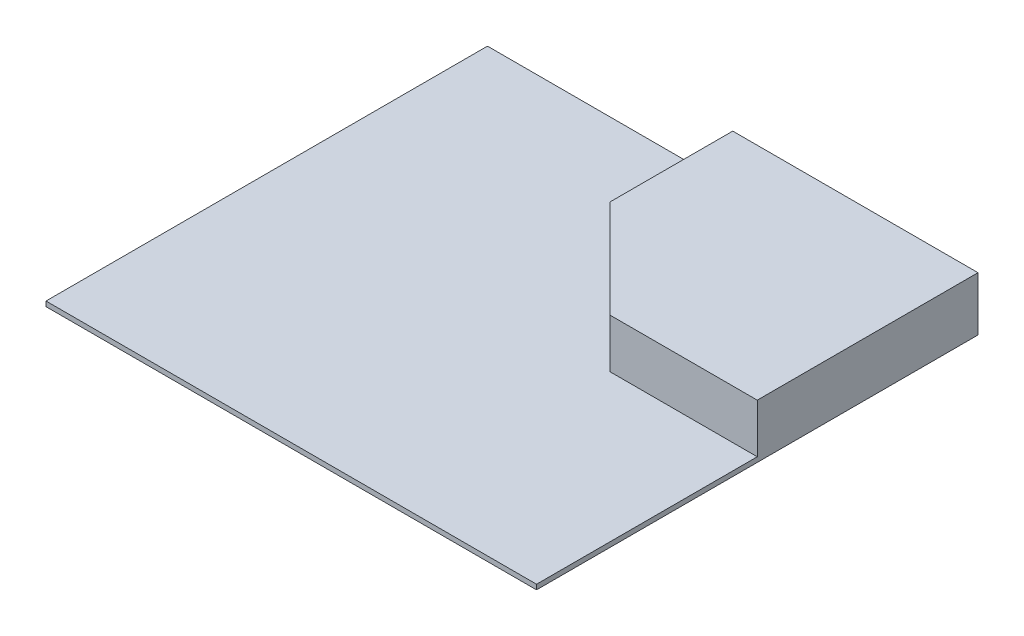
SolidWorks part; units mm, degrees
ref_plane "Front Plane" through (0, 0, 0) normal (0, 0, 1) x (1, 0, 0)
ref_plane "Top Plane" through (0, 0, 0) normal (0, 1, 0) x (1, 0, 0)
ref_plane "Right Plane" through (0, 0, 0) normal (1, 0, 0) x (0, 0, -1)
sketch "Sketch1" plane through (0, 0, 0) normal (0, 1, 0) x (1, 0, 0)
  line L1 (-500, 450) -> (500, 450)
  line L2 (-500, 450) -> (-500, -450)
  line L3 (-500, -450) -> (500, -450)
  line L4 (500, 450) -> (500, -450)
  line L5 (-500, 450) -> (500, -450) construction
  line L6 (-500, -450) -> (500, 450) construction
  point P0 (0, 0)
  dimension "D1" = 1000
  dimension "D2" = 900
extrude "Boss-Extrude1" add sketch "Sketch1" along normal blind 10 contours L2 L3 L4 L1
sketch "Sketch2" plane through (0, 10, 0) normal (0, 1, 0) x (1, 0, 0)
  line L0 (0, 450) -> (0, 200)
  line L1 (-500, 450) -> (500, 450) construction
  line L2 (0, 200) -> (200, 0)
  line L3 (200, 0) -> (500, 0)
  line L4 (500, 450) -> (500, -450) construction
  line L5 (500, 0) -> (500, 450)
  line L6 (500, 450) -> (0, 450)
  dimension "D1" = 250
  dimension "D2" = 300
extrude "Boss-Extrude2" add sketch "Sketch2" along normal blind 100
sketch3d "URDF Reference"
  line L0 (0, 0, 0) -> (10, 0, 0) construction
  line L1 (0, 0, 0) -> (0, 0, -10) construction
  point P0 (0, 0, 0)
  point P1 (0, 0, 0)
